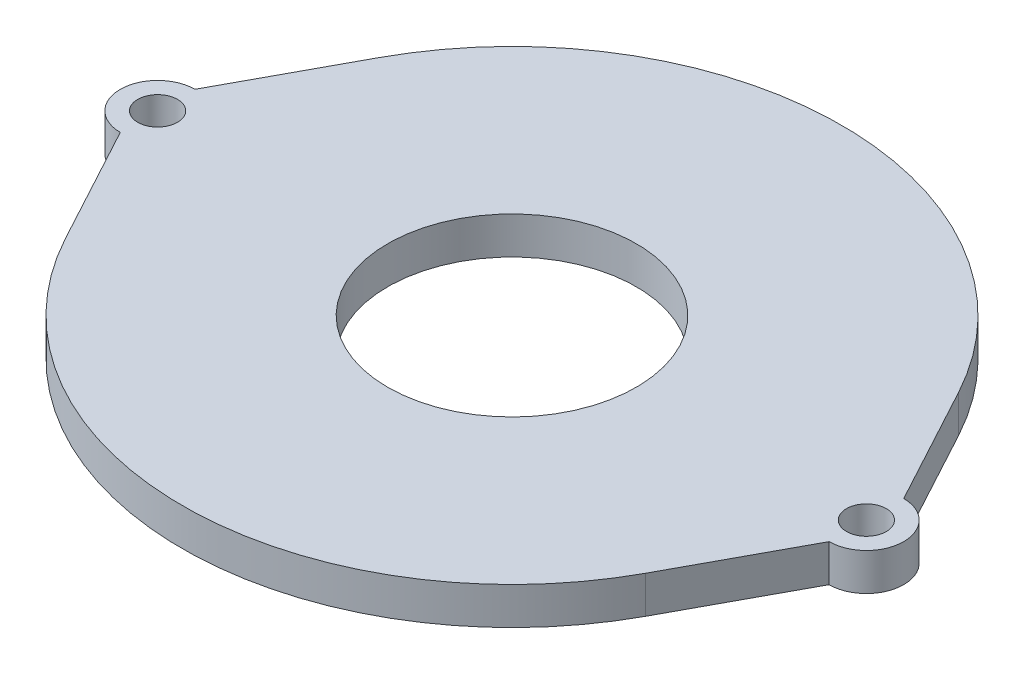
SolidWorks part; units mm, degrees
material "PLA"
ref_plane "Front Plane" through (0, 0, 0) normal (0, 0, 1) x (1, 0, 0)
ref_plane "Top Plane" through (0, 0, 0) normal (0, 1, 0) x (1, 0, 0)
ref_plane "Right Plane" through (0, 0, 0) normal (1, 0, 0) x (0, 0, -1)
sketch "Sketch1" plane through (0, 0, 0) normal (0, 1, 0) x (1, 0, 0)
  line L0 (-28.5, 3) -> (-23.3143, 12.5973)
  line L1 (-28.5, -3) -> (-23.3143, -12.5973)
  line L2 (28.5, -3) -> (23.3143, -12.5973)
  line L3 (28.5, 3) -> (23.3143, 12.5973)
  arc A0 (-23.3143, -12.5973) -> (23.3143, -12.5973) centre (0, 0) ccw
  arc A1 (28.5, -3) -> (28.5, 3) centre (28.5, 0) ccw
  arc A2 (-28.5, 3) -> (-28.5, -3) centre (-28.5, 0) ccw
  arc A3 (23.3143, 12.5973) -> (-23.3143, 12.5973) centre (0, 0) ccw
  circle A4 centre (0, 0) radius 10
  dimension "D1" = 53
  dimension "D4" = 6
  dimension "D5" = 20
  dimension "D2" = 1
  dimension "D3" = 1
extrude "Boss-Extrude1" add sketch "Sketch1" against normal blind 3
hole_wizard "M3 Clearance Hole1" positions "Sketch3" profile "Sketch4" hole size "M3" standard "ANSI Metric" end condition up to next
sketch "Sketch3" plane through (0, -3, 0) normal (0, -1, 0) x (-1, 0, 0)
  point P0 (-28.5, 0)
  point P3 (28.5, 0)
sketch "Sketch4" plane through (28.5, -3, 0) normal (1, 0, 0) x (0, 0, -1)
  line L0 (0, 0) -> (0, 3)
  line L1 (0, 3) -> (1.6, 3)
  line L2 (1.6, 3) -> (1.6, 0)
  line L5 (1.6, 0) -> (0, 0)
  line L11 (0, -6.35) -> (0, 107.95) construction
  dimension "Thru Hole Dia." = 3.2
  dimension "Thru Hole Depth" = 3
equation "\"D3@Sketch1\"=\"D2@Sketch1\""
